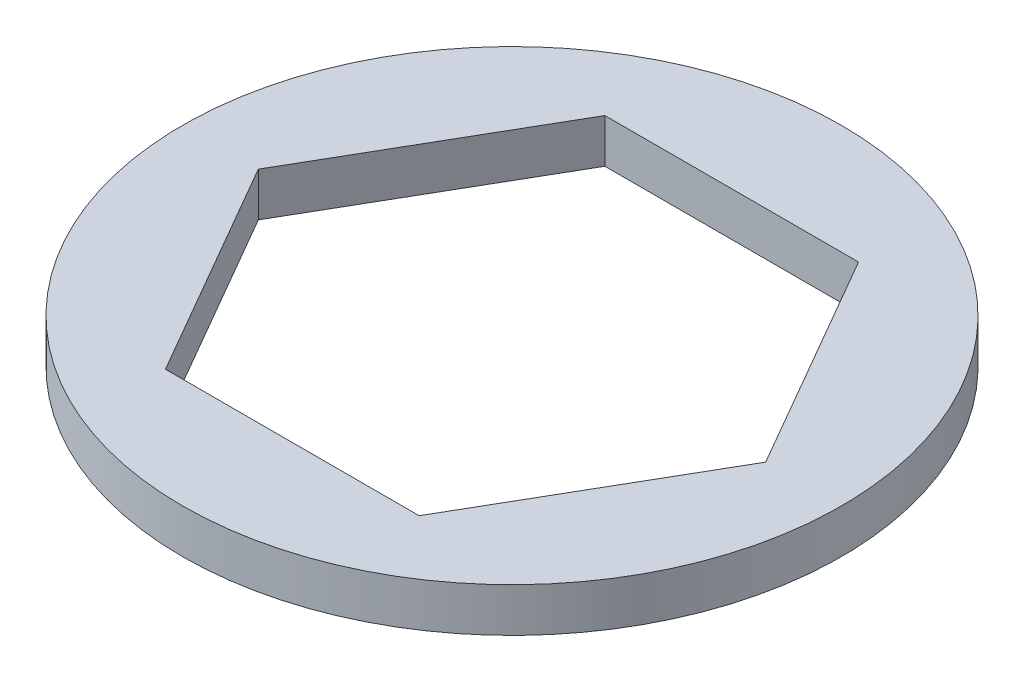
SolidWorks part; units mm, degrees
material "ABS"
ref_plane "Front Plane" through (0, 0, 0) normal (0, 0, 1) x (1, 0, 0)
ref_plane "Top Plane" through (0, 0, 0) normal (0, 1, 0) x (1, 0, 0)
ref_plane "Right Plane" through (0, 0, 0) normal (1, 0, 0) x (0, 0, -1)
sketch "Sketch1" plane through (0, 0, 0) normal (0, 1, 0) x (1, 0, 0)
  line L1 (3.6662, 6.35) -> (-3.6662, 6.35)
  line L2 (-3.6662, 6.35) -> (-7.3323, 0)
  line L3 (-7.3323, 0) -> (-3.6662, -6.35)
  line L4 (-3.6662, -6.35) -> (3.6662, -6.35)
  line L5 (3.6662, -6.35) -> (7.3323, 0)
  line L6 (7.3323, 0) -> (3.6662, 6.35)
  circle A0 centre (0, 0) radius 9.525
  circle A1 centre (0, 0) radius 6.35 construction
  dimension "D1" = 19.05
  dimension "D2" = 12.7
extrude "Boss-Extrude1" add sketch "Sketch1" along normal blind 1.27
